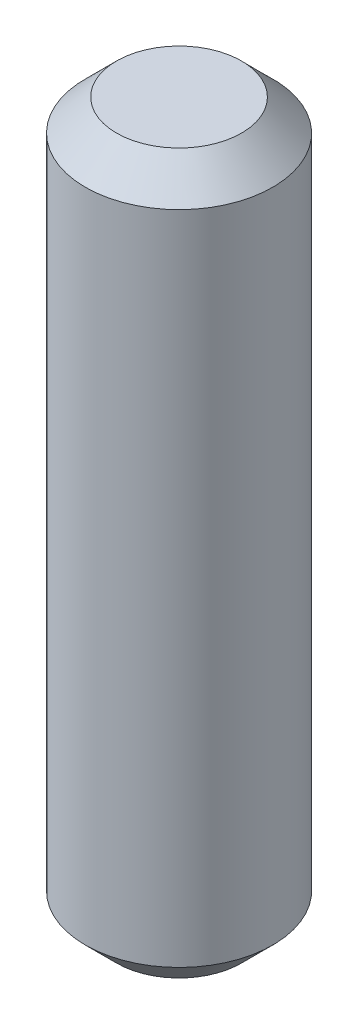
SolidWorks part; units mm, degrees
material "AISI 1045 Steel, cold drawn"
ref_plane "Alzado" through (0, 0, 0) normal (0, 0, 1) x (1, 0, 0)
ref_plane "Planta" through (0, 0, 0) normal (0, 1, 0) x (1, 0, 0)
ref_plane "Vista lateral" through (0, 0, 0) normal (1, 0, 0) x (0, 0, -1)
sketch "Sketch1" plane through (0, 0, 0) normal (0, 1, 0) x (1, 0, 0)
  circle A0 centre (0, 0) radius 3
  dimension "D1" = 6
extrude "Boss-Extrude1" add sketch "Sketch1" along normal blind 23
chamfer "Chamfer2" distance 1 angle 45 2 edges at (0, 23, 3) (0, 0, 3)
